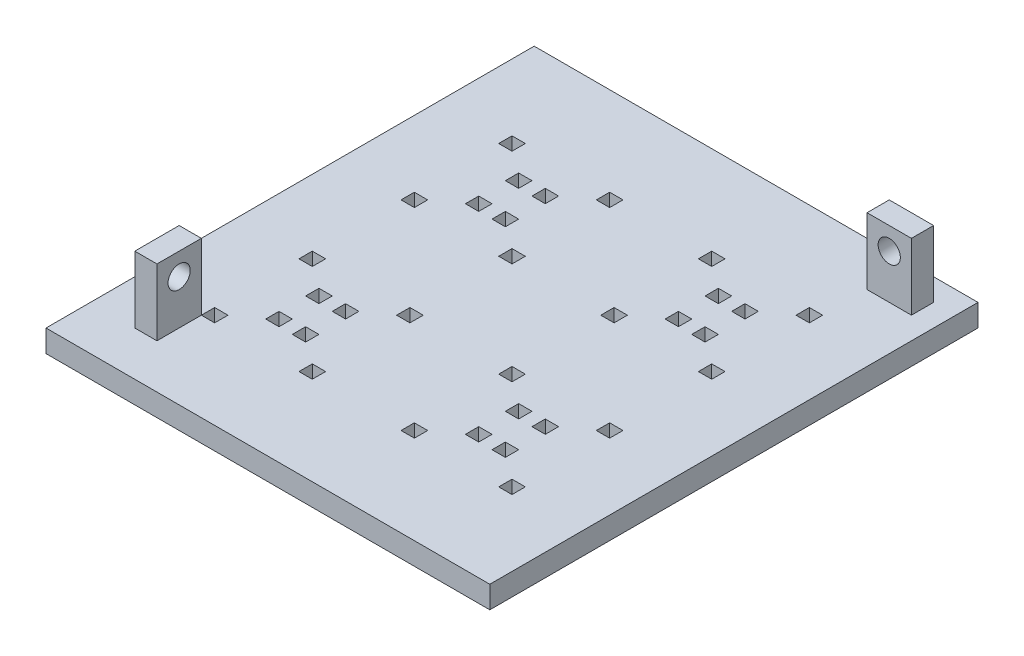
SolidWorks part; units mm, degrees
ref_plane "Front Plane" through (0, 0, 0) normal (0, 0, 1) x (1, 0, 0)
ref_plane "Top Plane" through (0, 0, 0) normal (0, 1, 0) x (1, 0, 0)
ref_plane "Right Plane" through (0, 0, 0) normal (1, 0, 0) x (0, 0, -1)
sketch "Sketch1" plane through (0, 0, 0) normal (0, 1, 0) x (1, 0, 0)
  line L0 (-50, 110) -> (-50, 0) construction
  line L1 (-100, 110) -> (0, 110)
  line L2 (-100, 110) -> (-100, 0)
  line L3 (-100, 0) -> (0, 0)
  line L4 (0, 110) -> (0, 0)
  line L5 (-40, 45) -> (-37, 45)
  line L6 (-40, 45) -> (-40, 42)
  line L7 (-40, 42) -> (-37, 42)
  line L8 (-37, 45) -> (-37, 42)
  line L9 (-18, 45) -> (-15, 45)
  line L10 (-18, 45) -> (-18, 42)
  line L11 (-18, 42) -> (-15, 42)
  line L12 (-15, 45) -> (-15, 42)
  line L13 (-40, 23) -> (-37, 23)
  line L14 (-40, 23) -> (-40, 20)
  line L15 (-40, 20) -> (-37, 20)
  line L16 (-37, 23) -> (-37, 20)
  line L17 (-18, 23) -> (-15, 23)
  line L18 (-18, 23) -> (-18, 20)
  line L19 (-18, 20) -> (-15, 20)
  line L20 (-15, 23) -> (-15, 20)
  line L21 (0, 55) -> (-100, 55) construction
  line L22 (-23, 26.5) -> (-18, 23) construction
  line L23 (-32, 38.5) -> (-29, 38.5)
  line L24 (-32, 38.5) -> (-32, 35.5)
  line L25 (-32, 35.5) -> (-29, 35.5)
  line L26 (-29, 38.5) -> (-29, 35.5)
  line L27 (-32, 29.5) -> (-29, 29.5)
  line L28 (-32, 29.5) -> (-32, 26.5)
  line L29 (-32, 26.5) -> (-29, 26.5)
  line L30 (-29, 29.5) -> (-29, 26.5)
  line L31 (-26, 38.5) -> (-23, 38.5)
  line L32 (-26, 38.5) -> (-26, 35.5)
  line L33 (-26, 35.5) -> (-23, 35.5)
  line L34 (-23, 38.5) -> (-23, 35.5)
  line L35 (-26, 29.5) -> (-23, 29.5)
  line L36 (-26, 29.5) -> (-26, 26.5)
  line L37 (-26, 26.5) -> (-23, 26.5)
  line L38 (-23, 29.5) -> (-23, 26.5)
  line L39 (-32, 26.5) -> (-37, 23) construction
  line L40 (-37, 42) -> (-32, 38.5) construction
  line L41 (-18, 42) -> (-23, 38.5) construction
  line L42 (-82, 42) -> (-77, 38.5) construction
  line L43 (-63, 42) -> (-68, 38.5) construction
  line L44 (-68, 26.5) -> (-63, 23) construction
  line L45 (-77, 26.5) -> (-82, 23) construction
  line L46 (-77, 29.5) -> (-77, 26.5)
  line L47 (-74, 26.5) -> (-77, 26.5)
  line L48 (-74, 29.5) -> (-74, 26.5)
  line L49 (-74, 29.5) -> (-77, 29.5)
  line L50 (-77, 38.5) -> (-77, 35.5)
  line L51 (-74, 35.5) -> (-77, 35.5)
  line L52 (-74, 38.5) -> (-74, 35.5)
  line L53 (-74, 38.5) -> (-77, 38.5)
  line L54 (-71, 29.5) -> (-71, 26.5)
  line L55 (-68, 26.5) -> (-71, 26.5)
  line L56 (-68, 29.5) -> (-68, 26.5)
  line L57 (-68, 29.5) -> (-71, 29.5)
  line L58 (-71, 38.5) -> (-71, 35.5)
  line L59 (-68, 35.5) -> (-71, 35.5)
  line L60 (-68, 38.5) -> (-68, 35.5)
  line L61 (-68, 38.5) -> (-71, 38.5)
  line L62 (-85, 23) -> (-85, 20)
  line L63 (-82, 20) -> (-85, 20)
  line L64 (-82, 23) -> (-82, 20)
  line L65 (-82, 23) -> (-85, 23)
  line L66 (-63, 23) -> (-63, 20)
  line L67 (-60, 20) -> (-63, 20)
  line L68 (-60, 23) -> (-60, 20)
  line L69 (-60, 23) -> (-63, 23)
  line L70 (-85, 45) -> (-85, 42)
  line L71 (-82, 42) -> (-85, 42)
  line L72 (-82, 45) -> (-82, 42)
  line L73 (-82, 45) -> (-85, 45)
  line L74 (-63, 45) -> (-63, 42)
  line L75 (-60, 42) -> (-63, 42)
  line L76 (-60, 45) -> (-60, 42)
  line L77 (-60, 45) -> (-63, 45)
  line L78 (-77, 83.5) -> (-82, 87) construction
  line L79 (-68, 83.5) -> (-63, 87) construction
  line L80 (-63, 68) -> (-68, 71.5) construction
  line L81 (-82, 68) -> (-77, 71.5) construction
  line L82 (-18, 68) -> (-23, 71.5) construction
  line L83 (-37, 68) -> (-32, 71.5) construction
  line L84 (-32, 83.5) -> (-37, 87) construction
  line L85 (-23, 83.5) -> (-18, 87) construction
  line L86 (-60, 65) -> (-63, 65)
  line L87 (-60, 65) -> (-60, 68)
  line L88 (-60, 68) -> (-63, 68)
  line L89 (-63, 65) -> (-63, 68)
  line L90 (-82, 65) -> (-85, 65)
  line L91 (-82, 65) -> (-82, 68)
  line L92 (-82, 68) -> (-85, 68)
  line L93 (-85, 65) -> (-85, 68)
  line L94 (-60, 87) -> (-63, 87)
  line L95 (-60, 87) -> (-60, 90)
  line L96 (-60, 90) -> (-63, 90)
  line L97 (-63, 87) -> (-63, 90)
  line L98 (-82, 87) -> (-85, 87)
  line L99 (-82, 87) -> (-82, 90)
  line L100 (-82, 90) -> (-85, 90)
  line L101 (-85, 87) -> (-85, 90)
  line L102 (-68, 71.5) -> (-71, 71.5)
  line L103 (-68, 71.5) -> (-68, 74.5)
  line L104 (-68, 74.5) -> (-71, 74.5)
  line L105 (-71, 71.5) -> (-71, 74.5)
  line L106 (-68, 80.5) -> (-71, 80.5)
  line L107 (-68, 80.5) -> (-68, 83.5)
  line L108 (-68, 83.5) -> (-71, 83.5)
  line L109 (-71, 80.5) -> (-71, 83.5)
  line L110 (-74, 71.5) -> (-77, 71.5)
  line L111 (-74, 71.5) -> (-74, 74.5)
  line L112 (-74, 74.5) -> (-77, 74.5)
  line L113 (-77, 71.5) -> (-77, 74.5)
  line L114 (-74, 80.5) -> (-77, 80.5)
  line L115 (-74, 80.5) -> (-74, 83.5)
  line L116 (-74, 83.5) -> (-77, 83.5)
  line L117 (-77, 80.5) -> (-77, 83.5)
  line L118 (-23, 80.5) -> (-23, 83.5)
  line L119 (-26, 83.5) -> (-23, 83.5)
  line L120 (-26, 80.5) -> (-26, 83.5)
  line L121 (-26, 80.5) -> (-23, 80.5)
  line L122 (-23, 71.5) -> (-23, 74.5)
  line L123 (-26, 74.5) -> (-23, 74.5)
  line L124 (-26, 71.5) -> (-26, 74.5)
  line L125 (-26, 71.5) -> (-23, 71.5)
  line L126 (-29, 80.5) -> (-29, 83.5)
  line L127 (-32, 83.5) -> (-29, 83.5)
  line L128 (-32, 80.5) -> (-32, 83.5)
  line L129 (-32, 80.5) -> (-29, 80.5)
  line L130 (-29, 71.5) -> (-29, 74.5)
  line L131 (-32, 74.5) -> (-29, 74.5)
  line L132 (-32, 71.5) -> (-32, 74.5)
  line L133 (-32, 71.5) -> (-29, 71.5)
  line L134 (-15, 87) -> (-15, 90)
  line L135 (-18, 90) -> (-15, 90)
  line L136 (-18, 87) -> (-18, 90)
  line L137 (-18, 87) -> (-15, 87)
  line L138 (-37, 87) -> (-37, 90)
  line L139 (-40, 90) -> (-37, 90)
  line L140 (-40, 87) -> (-40, 90)
  line L141 (-40, 87) -> (-37, 87)
  line L142 (-15, 65) -> (-15, 68)
  line L143 (-18, 68) -> (-15, 68)
  line L144 (-18, 65) -> (-18, 68)
  line L145 (-18, 65) -> (-15, 65)
  line L146 (-37, 65) -> (-37, 68)
  line L147 (-40, 68) -> (-37, 68)
  line L148 (-40, 65) -> (-40, 68)
  line L149 (-40, 65) -> (-37, 65)
  point P24 (-50, 110)
  point P26 (0, 55)
  point P43 (-19.0127, 29.9432)
  point P44 (-26.8949, 24.7744)
  point P45 (-30.8538, 38.1578)
  dimension "D1" = 110
  dimension "D2" = 100
  dimension "D3" = 3
  dimension "D4" = 3
  dimension "D5" = 3
  dimension "D6" = 3
  dimension "D7" = 3
  dimension "D8" = 3
  dimension "D9" = 3
  dimension "D10" = 25
  dimension "D11" = 25
  dimension "D12" = 25
  dimension "D13" = 25
  dimension "D14" = 3
  dimension "D15" = 3
  dimension "D16" = 3
  dimension "D17" = 3
  dimension "D18" = 3
  dimension "D19" = 3
  dimension "D20" = 3
  dimension "D21" = 3
  dimension "D22" = 6
  dimension "D23" = 3
  dimension "D24" = 6
  dimension "D25" = 3
  dimension "D26" = 20
  dimension "D27" = 20
extrude "Boss-Extrude1" add sketch "Sketch1" along normal blind 5
sketch "Sketch2" plane through (0, 5, 0) normal (0, 1, 0) x (1, 0, 0)
  line L1 (-15, 105) -> (-5, 105)
  line L2 (-15, 105) -> (-15, 100)
  line L3 (-15, 100) -> (-5, 100)
  line L4 (-5, 105) -> (-5, 100)
  line L6 (0, 110) -> (-100, 110) construction
  line L7 (0, 0) -> (0, 110) construction
  line L8 (-100, 110) -> (-100, 0) construction
  line L9 (-90, 20) -> (-85, 20)
  line L10 (-90, 20) -> (-90, 10)
  line L11 (-90, 10) -> (-85, 10)
  line L12 (-85, 20) -> (-85, 10)
  line L13 (-100, 0) -> (0, 0) construction
  point P14 (-5, 102.5)
  dimension "D1" = 10
  dimension "D2" = 5
  dimension "D3" = 5
  dimension "D4" = 5
  dimension "D5" = 5
  dimension "D6" = 10
  dimension "D7" = 10
  dimension "D8" = 10
extrude "Boss-Extrude2" add sketch "Sketch2" along normal blind 15
sketch "Sketch3" plane through (0, 0, -105) normal (0, 0, -1) x (-1, 0, 0)
  line L0 (5, 20) -> (15, 20) construction
  line L1 (5, 5) -> (15, 5) construction
  circle A0 centre (10, 15) radius 2.5
  point P4 (10, 20)
  dimension "D1" = 5
  dimension "D2" = 10
extrude "Cut-Extrude1" cut sketch "Sketch3" against normal blind 15
sketch "Sketch5" plane through (-90, 0, 0) normal (-1, 0, 0) x (0, 0, 1)
  line L0 (-20, 20) -> (-10, 20) construction
  line L1 (-20, 5) -> (-10, 5) construction
  circle A0 centre (-15, 15) radius 2.5
  point P4 (-15, 20)
  dimension "D1" = 5
  dimension "D2" = 10
extrude "Cut-Extrude2" cut sketch "Sketch5" against normal blind 15
